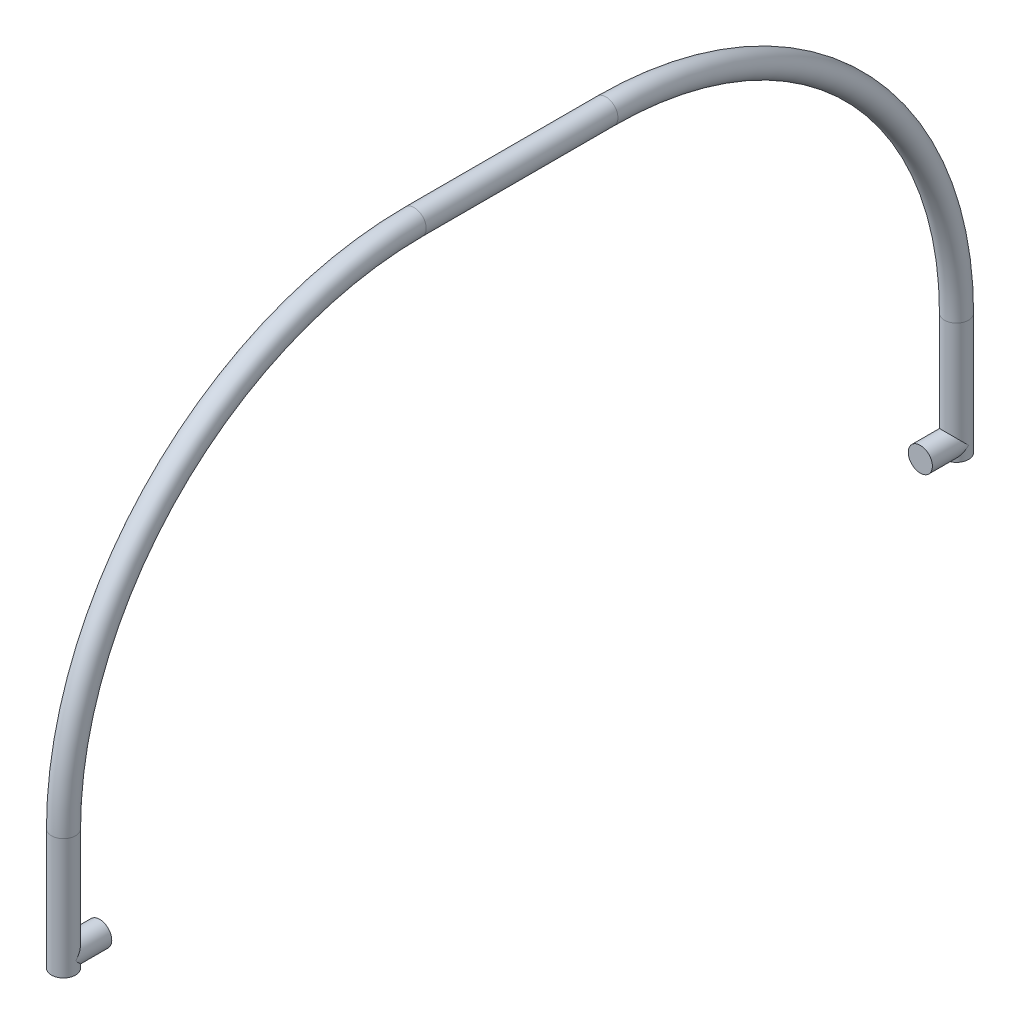
SolidWorks part; units mm, degrees
ref_plane "Front Plane" through (0, 0, 0) normal (0, 0, 1) x (1, 0, 0)
ref_plane "Top Plane" through (0, 0, 0) normal (0, 1, 0) x (1, 0, 0)
ref_plane "Right Plane" through (0, 0, 0) normal (1, 0, 0) x (0, 0, -1)
sketch "Sketch1" plane through (0, 0, 0) normal (1, 0, 0) x (0, 0, -1)
  line L0 (-185, 0) -> (185, 0) construction
  line L1 (-185, 0) -> (-185, 50)
  line L2 (-39.7196, 195.2804) -> (39.7196, 195.2804)
  line L3 (185, 50) -> (185, 0)
  line L4 (0, 162.1946) -> (0, -93.0012) construction
  arc A0 (-185, 50) -> (-39.7196, 195.2804) centre (-39.7196, 50) cw
  arc A1 (39.7196, 195.2804) -> (185, 50) centre (39.7196, 50) cw
  point P9 (-75.3891, 148.099)
  point P11 (78.264, 143.1602)
  point P15 (-64.9626, 147.5503)
  dimension "D1" = 370
  dimension "D2" = 50
sketch "Sketch2" plane through (0, 0, 0) normal (0, 1, 0) x (1, 0, 0)
  line L0 (0, 39.7196) -> (0, 185) construction
  line L1 (0, -185) -> (0, 185) construction
  circle A0 centre (0, 185) radius 5
  point P6 (0, 131.6613)
  point P7 (0, 185)
sweep "Sweep2" add profiles "Sketch2" path "Sketch1"
ref_plane "Plane1" through (0, 0, 180) normal (0, 0, 1) x (1, 0, 0)
sketch "Sketch3" plane through (0, 0, 180) normal (0, 0, 1) x (1, 0, 0)
  circle A0 centre (0, 5.0317) radius 5
  point P2 (0, 5.0317)
extrude "Boss-Extrude1" add sketch "Sketch3" against normal blind 10 and the other way up to surface separate body
ref_plane "Plane2" through (0, 0, -180) normal (0, 0, 1) x (1, 0, 0)
sketch "Sketch4" plane through (0, 0, -180) normal (0, 0, 1) x (1, 0, 0)
  circle A0 centre (0, 5.1106) radius 5
  point P2 (0, 5.1106)
extrude "Boss-Extrude2" add sketch "Sketch4" along normal blind 10 and the other way up to surface
